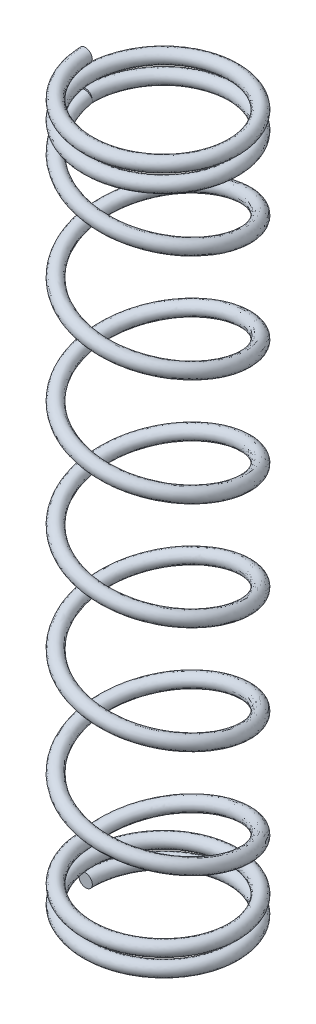
SolidWorks part; units mm, degrees
ref_plane "Front Plane" through (0, 0, 0) normal (0, 0, 1) x (1, 0, 0)
ref_plane "Top Plane" through (0, 0, 0) normal (0, 1, 0) x (1, 0, 0)
ref_plane "Right Plane" through (0, 0, 0) normal (1, 0, 0) x (0, 0, -1)
sketch "Sketch1" plane through (0, 0, 0) normal (0, 1, 0) x (1, 0, 0)
  circle A0 centre (0, 0) radius 2.7
  dimension "D1" = 5.4
curve "Helix/Spiral2" pitch 4 height 24 turns 6
sketch "Sketch2" plane through (0, 0, 0) normal (0, 1, 0) x (1, 0, 0)
  circle A0 centre (0, 0) radius 2.6983
  dimension "D1" = 5.3966
curve "Helix/Spiral3" pitch 0.66 height 1.32 turns 2
ref_plane "Plane2" through (0, 24, 0) normal (0, 1, 0) x (1, 0, 0)
sketch "Sketch3" plane through (0, 24, 0) normal (0, 1, 0) x (1, 0, 0)
  circle A0 centre (0, 0) radius 2.7
  dimension "D1" = 5.4
curve "Helix/Spiral4" pitch 0.66 height 1.32 turns 2
sweep "Sweep1" add path "Helix/Spiral4" circular profile diameter 0.5 parameters "D3"=0.5
sweep "Sweep2" add path "Helix/Spiral2" circular profile diameter 0.5 parameters "D3"=0.5
sweep "Sweep3" add path "Helix/Spiral3" circular profile diameter 0.5 parameters "D3"=0.5
sketch "Sketch4" plane through (0, 0, 0) normal (0, 0, 1) x (1, 0, 0)
  line L0 (0, 0) -> (0, 32.3514) construction
  line L1 (0, 32.3514) -> (0, 0)
  dimension "D1" = 32.3514
